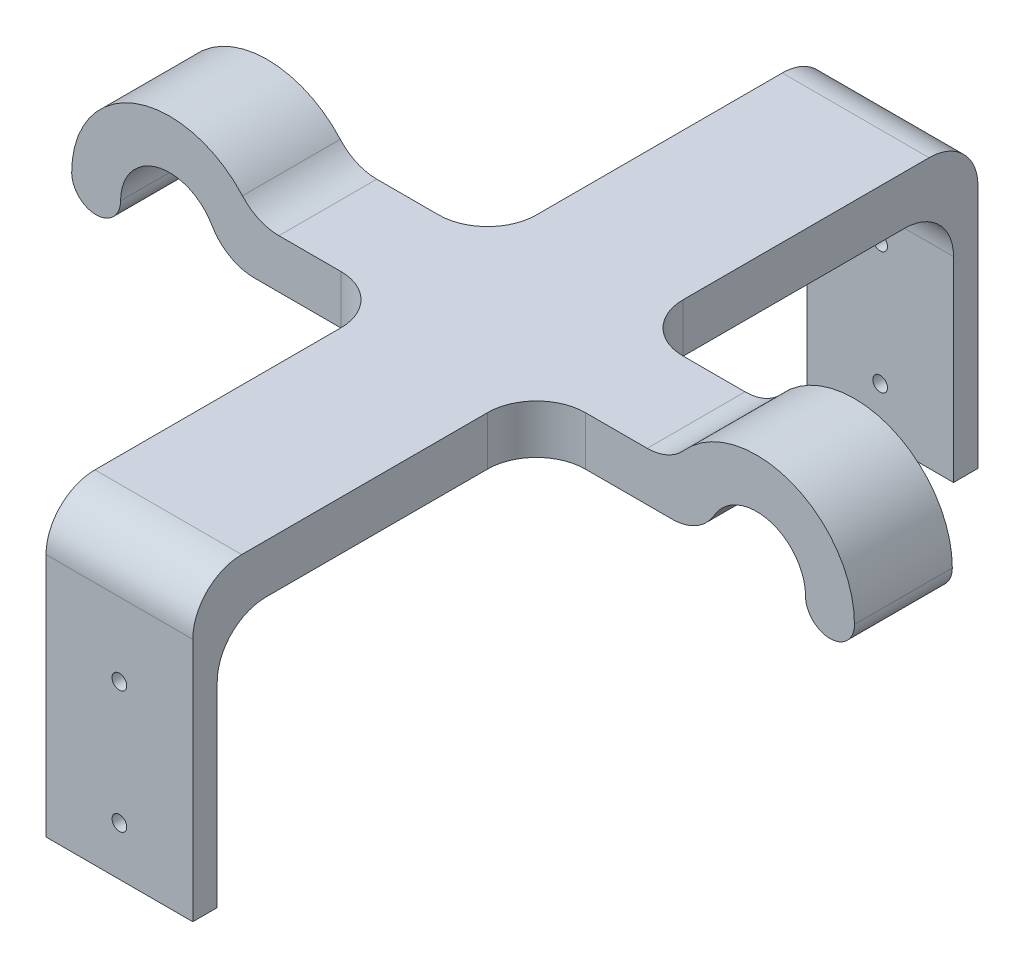
SolidWorks part; units mm, degrees
ref_plane "Front Plane" through (0, 0, 0) normal (0, 0, 1) x (1, 0, 0)
ref_plane "Top Plane" through (0, 0, 0) normal (0, 1, 0) x (1, 0, 0)
ref_plane "Right Plane" through (0, 0, 0) normal (1, 0, 0) x (0, 0, -1)
sketch "Sketch1" plane through (0, 0, 0) normal (0, 0, 1) x (1, 0, 0)
  line L0 (-60, 0) -> (60, 0) construction
  line L1 (-80, 0) -> (80, 0) construction
  line L2 (-50, 0) -> (50, 0)
  line L3 (-42.6795, 10) -> (42.6795, 10)
  arc A0 (-50, 0) -> (-70, 0) centre (-60, 0) ccw
  arc A1 (70, 0) -> (50, 0) centre (60, 0) ccw
  arc A2 (-40, 0) -> (-80, 0) centre (-60, 0) ccw
  arc A3 (80, 0) -> (40, 0) centre (60, 0) ccw
  arc A4 (-70, 0) -> (-80, 0) centre (-75, 0) cw
  circle A5 centre (-60, 0) radius 20 construction
  circle A6 centre (-60, 0) radius 10 construction
  circle A7 centre (60, 0) radius 10 construction
  circle A8 centre (60, 0) radius 20 construction
  arc A9 (70, 0) -> (80, 0) centre (75, 0) ccw
  point P3 (0, 0)
  point P4 (79.6462, 6.0065)
  point P5 (90.5439, 0)
  point P12 (-29.4561, 0)
  point P14 (-40.3538, 6.0065)
  dimension "D3" = 10
  dimension "D1" = 120
  dimension "D4" = 10
  dimension "D2" = 10
extrude "Boss-Extrude1" add sketch "Sketch1" along normal mid plane 20 contours A4 A0 L2 A2 | A3 L3 A2 L2 | A1 A9 A3 L2
sketch "Sketch2" plane through (0, 0, 0) normal (0, -1, 0) x (1, 0, 0)
  line L0 (0, 80.25) -> (0, -80.25) construction
  line L2 (-15, -80.25) -> (15, -80.25)
  line L3 (-15, -80.25) -> (-15, 80.25)
  line L4 (-15, 80.25) -> (15, 80.25)
  line L5 (15, -80.25) -> (15, 80.25)
  line L6 (-15, -80.25) -> (15, 80.25) construction
  line L7 (-15, 80.25) -> (15, -80.25) construction
  point P2 (0, 0)
  point P3 (0, -80.25)
  point P5 (0, 0)
  dimension "D1" = 160.5
  dimension "D2" = 30
extrude "Boss-Extrude2" add sketch "Sketch2" against normal blind 10
sketch "Sketch3" plane through (0, 0, 0) normal (0, -1, 0) x (1, 0, 0)
  line L0 (15, 10) -> (15, 80.25) construction
  line L1 (-15, 80.25) -> (15, 80.25)
  line L2 (-15, 80.25) -> (-15, 75.25)
  line L3 (-15, 75.25) -> (15, 75.25)
  line L4 (15, 80.25) -> (15, 75.25)
  dimension "D1" = 5
extrude "Boss-Extrude3" add sketch "Sketch3" along normal blind 50
mirror "Mirror1" about plane through (0, 0, 0) normal (0, 0, 1) of "Boss-Extrude3"
sketch "Sketch4" plane through (0, 0, 80.25) normal (0, 0, 1) x (1, 0, 0)
  line L0 (0, 10) -> (0, -50) construction
  line L1 (15, 10) -> (-15, 10) construction
  line L2 (15, -50) -> (-15, -50) construction
  circle A0 centre (0, -40) radius 1.5
  circle A1 centre (0, -15) radius 1.5
  dimension "D1" = 25
  dimension "D2" = 3
  dimension "D3" = 10
extrude "Cut-Extrude1" cut sketch "Sketch4" against normal through all both and the other way through all contours A0 L0 | L0 A0 | A1
fillet "Fillet1" radius 10 4 edges at (0, 10, -80.25) (0, 0, -75.25) (0, 0, 75.25) (0, 10, 80.25)
fillet "Fillet2" radius 10 4 edges at (-15, 5, -10) (15, 5, -10) (15, 5, 10) (-15, 5, 10)
fillet "Fillet3" radius 10 4 edges at (42.6795, 10, 0) (-42.6795, 10, 0) (-50, 0, 0) (50, 0, 0)
